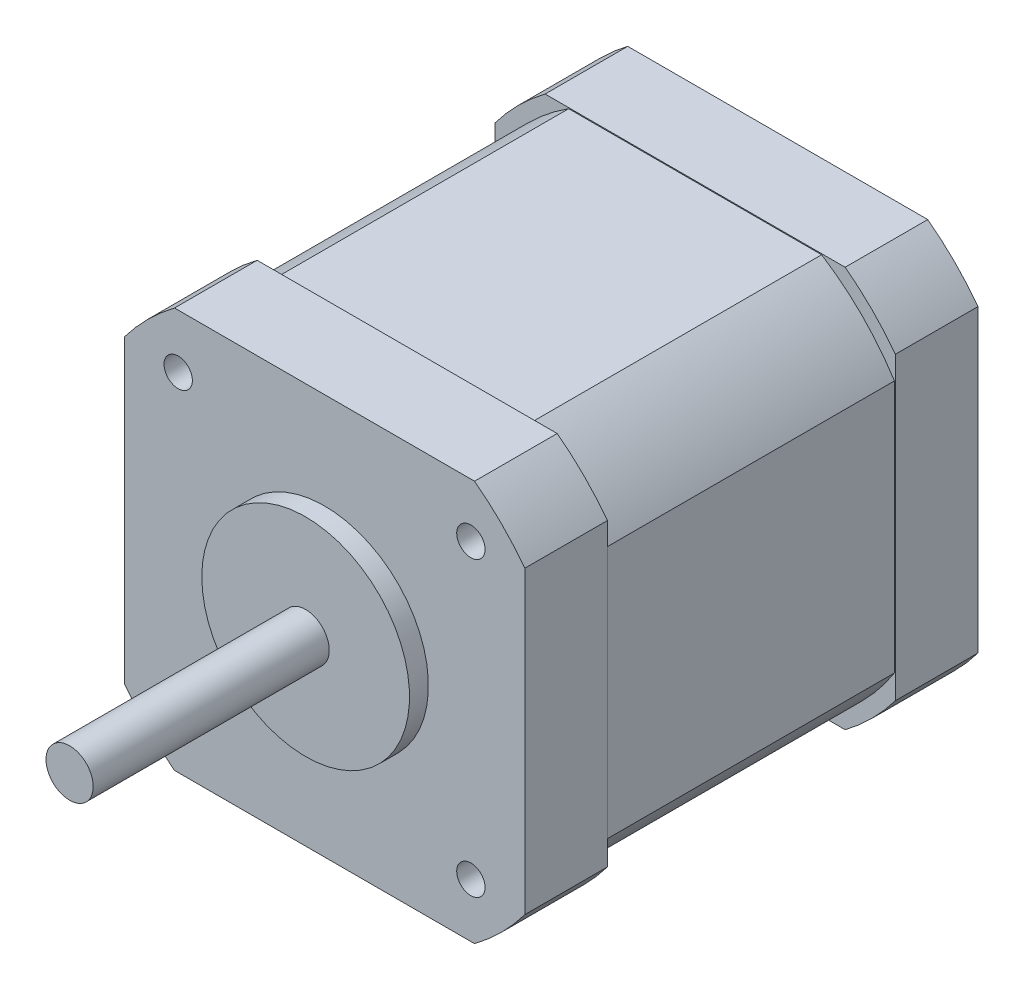
SolidWorks part; units mm, degrees
material "Plain Carbon Steel"
ref_plane "Front" through (0, 0, 0) normal (0, 0, 1) x (1, 0, 0)
ref_plane "Top" through (0, 0, 0) normal (0, 1, 0) x (1, 0, 0)
ref_plane "Right" through (0, 0, 0) normal (1, 0, 0) x (0, 0, -1)
sketch "Sketch1" plane through (0, 0, 0) normal (0, 0, 1) x (1, 0, 0)
  circle A0 centre (0, 0) radius 2.5
  dimension "D1" = 5
extrude "Boss-Extrude1" add sketch "Sketch1" along normal blind 27
sketch "Sketch2" plane through (0, 0, 0) normal (0, 0, -1) x (-1, 0, 0)
  circle A0 centre (0, 0) radius 11
  dimension "D1" = 22
extrude "Boss-Extrude2" add sketch "Sketch2" against normal blind 2
sketch "Sketch3" plane through (0, 0, 0) normal (0, 0, -1) x (-1, 0, 0)
  line L1 (21.209, -21.209) -> (-21.209, -21.209)
  line L2 (21.209, -21.209) -> (21.209, 21.209)
  line L3 (21.209, 21.209) -> (-21.209, 21.209)
  line L4 (-21.209, -21.209) -> (-21.209, 21.209)
  line L5 (21.209, -21.209) -> (-21.209, 21.209) construction
  line L6 (21.209, 21.209) -> (-21.209, -21.209) construction
  point P0 (0, 0)
  dimension "D1" = 42.418
extrude "Boss-Extrude3" add sketch "Sketch3" along normal blind 48
sketch "Sketch4" plane through (0, 0, -48) normal (0, 0, -1) x (-1, 0, 0)
  line L0 (-21.209, -15.888) -> (-21.209, -21.209)
  line L1 (15.888, -21.209) -> (21.209, -21.209)
  line L2 (21.209, 15.888) -> (21.209, 21.209)
  line L3 (-15.888, 21.209) -> (-21.209, 21.209)
  line L4 (-21.209, 21.209) -> (-21.209, -21.209)
  line L5 (-21.209, -21.209) -> (21.209, -21.209)
  line L6 (21.209, -21.209) -> (21.209, 21.209)
  line L7 (21.209, 21.209) -> (-21.209, 21.209)
  line L8 (-21.209, 21.209) -> (-21.209, 15.888)
  line L9 (-21.209, -21.209) -> (-15.888, -21.209)
  line L10 (21.209, -21.209) -> (21.209, -15.888)
  line L11 (21.209, 21.209) -> (15.888, 21.209)
  arc A0 (-21.209, -15.888) -> (-15.888, -21.209) centre (0, 0) ccw
  arc A1 (15.888, -21.209) -> (21.209, -15.888) centre (0, 0) ccw
  arc A2 (21.209, 15.888) -> (15.888, 21.209) centre (0, 0) ccw
  arc A3 (-15.888, 21.209) -> (-21.209, 15.888) centre (0, 0) ccw
  dimension "D2" = 26.5
  dimension "D1" = 0
extrude "Cut-Extrude1" cut sketch "Sketch4" against normal through all
hole_wizard "M3x0.5 Tapped Hole1" positions "Sketch6" profile "Sketch5" tap size "M3x0.5" standard "ANSI Metric"
sketch "Sketch6" plane through (0, 0, 0) normal (0, 0, 1) x (1, 0, 0)
  line L0 (-16.1632, 0) -> (0, 0) construction
  line L1 (0, 0) -> (0, 15.0764) construction
  point P0 (-15.5, 15.5)
  point P11 (-15.5, -15.5)
  point P12 (15.5, -15.5)
  point P13 (15.5, 15.5)
  dimension "D1" = 31
  dimension "D2" = 31
sketch "Sketch5" plane through (-15.5, 15.5, 0) normal (1, 0, 0) x (0, -1, 0)
  line L0 (0, 0) -> (0, 8.2511)
  line L1 (0, 8.2511) -> (1.25, 7.5)
  line L2 (1.25, 7.5) -> (1.25, 6)
  line L3 (1.25, 6) -> (1.5, 6)
  line L4 (1.5, 6) -> (1.5, 0)
  line L5 (1.5, 0) -> (0, 0)
  line L10 (0, 8.2511) -> (-1.25, 7.5) construction
  line L11 (0, -6.35) -> (0, 107.95) construction
  dimension "Tap Drill Dia." = 2.5
  dimension "Tap Drill Depth" = 7.5
  dimension "Thread Major Dia." = 3
  dimension "Thread Depth" = 6
  dimension "Drill Angle" = 118
sketch "Sketch7" plane through (0, 0, 27) normal (0, 0, 1) x (1, 0, 0)
  line L0 (-1.5, 2) -> (1.5, 2)
  circle A0 centre (0, 0) radius 2.5 construction
  circle A1 centre (0, 0) radius 2.5 construction
  arc A2 (1.5, 2) -> (-1.5, 2) centre (0, 0) ccw
  dimension "D1" = 4.5
extrude "Cut-Extrude2" [suppressed] cut sketch "Sketch7" against normal blind 15
ref_plane "Plane1" through (0, 0, -24) normal (0, 0, 1) x (1, 0, 0)
sketch "Sketch8" plane through (0, 0, -24) normal (0, 0, 1) x (1, 0, 0)
  line L0 (-13.3944, 21.109) -> (13.3944, 21.109)
  line L1 (-5.7152, 0) -> (0, 0) construction
  line L2 (0, 0) -> (0, 8.4579) construction
  line L3 (-15.888, 21.209) -> (15.888, 21.209) construction
  line L4 (-13.3944, -21.109) -> (13.3944, -21.109)
  line L5 (-21.109, 13.3944) -> (-21.109, -13.3944)
  line L6 (-21.209, -15.888) -> (-21.209, 15.888) construction
  line L7 (21.109, 13.3944) -> (21.109, -13.3944)
  line L12 (15.888, 21.209) -> (-15.888, 21.209)
  line L13 (-21.209, 15.888) -> (-21.209, -15.888)
  line L14 (-15.888, -21.209) -> (15.888, -21.209)
  line L15 (21.209, -15.888) -> (21.209, 15.888)
  line L16 (15.888, 21.209) -> (-15.888, 21.209)
  line L17 (-21.209, 15.888) -> (-21.209, -15.888)
  line L18 (-15.888, -21.209) -> (15.888, -21.209)
  line L19 (21.209, -15.888) -> (21.209, 15.888)
  arc A0 (-13.3944, 21.109) -> (-21.109, 13.3944) centre (0, 0) ccw
  arc A1 (-21.109, -13.3944) -> (-13.3944, -21.109) centre (0, 0) ccw
  arc A2 (21.109, 13.3944) -> (13.3944, 21.109) centre (0, 0) ccw
  arc A3 (13.3944, -21.109) -> (21.109, -13.3944) centre (0, 0) ccw
  arc A5 (-15.888, 21.209) -> (-21.209, 15.888) centre (0, 0) ccw
  arc A6 (-21.209, -15.888) -> (-15.888, -21.209) centre (0, 0) ccw
  arc A7 (15.888, -21.209) -> (21.209, -15.888) centre (0, 0) ccw
  arc A8 (21.209, 15.888) -> (15.888, 21.209) centre (0, 0) ccw
  arc A9 (-15.888, 21.209) -> (-21.209, 15.888) centre (0, 0) ccw
  arc A10 (-21.209, -15.888) -> (-15.888, -21.209) centre (0, 0) ccw
  arc A11 (15.888, -21.209) -> (21.209, -15.888) centre (0, 0) ccw
  arc A12 (21.209, 15.888) -> (15.888, 21.209) centre (0, 0) ccw
  dimension "D1" = 50
  dimension "D2" = 0.1
  dimension "D3" = 0.1
  dimension "D4" = 0
extrude "Cut-Extrude3" cut sketch "Sketch8" against normal offset from surface 8.75 and the other way offset from surface (15.25 mm away) 8.75 up to face at (0, 0, -48) other way up to face at (-14, 15.5, 0)
sketch "Sketch9" plane through (0, -21.209, 0) normal (0, -1, 0) x (1, 0, 0)
  line L0 (15.888, -48) -> (-15.888, -48) construction
  line L1 (-8, -48) -> (8, -48)
  line L2 (-8, -48) -> (-8, -43.5)
  line L3 (-8, -43.5) -> (8, -43.5)
  line L4 (8, -48) -> (8, -43.5)
  line L5 (0, -1000) -> (0, 49000) construction
  line L6 (15.888, 0) -> (-15.888, 0) construction
  point P7 (0, -43.5)
  point P11 (0, 0)
  dimension "D1" = 16
  dimension "D2" = 4.5
extrude "Boss-Extrude4" add sketch "Sketch9" along normal blind 4.75
